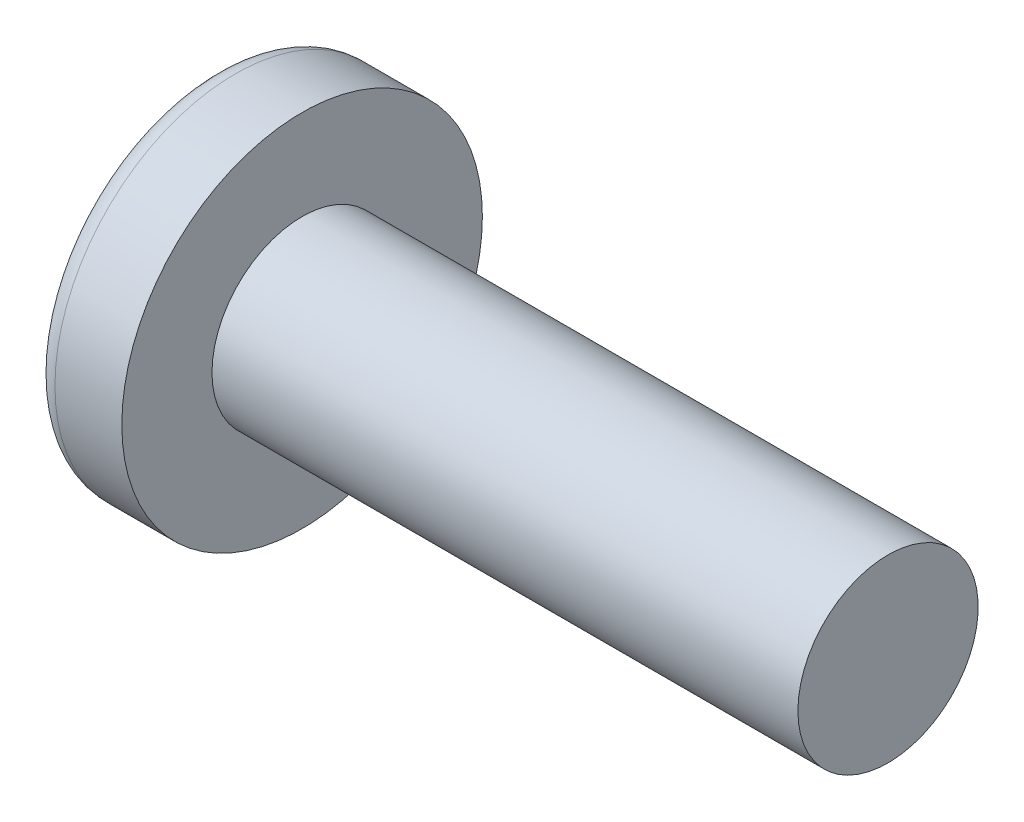
SolidWorks part; units mm, degrees
ref_plane "Plane1" through (0, 0, 0) normal (0, 0, 1) x (1, 0, 0)
ref_plane "Plane2" through (0, 0, 0) normal (0, 1, 0) x (1, 0, 0)
ref_plane "Plane3" through (0, 0, 0) normal (1, 0, 0) x (0, 0, -1)
other "Configuration Table"
sketch "BodySke" plane through (0, 0, 0) normal (0, 0, 1) x (1, 0, 0)
  line L0 (3.1, 2) -> (3.1, 4)
  line L1 (3.8, 6.35) -> (3.8, -3.175) construction
  line L2 (-25.4, 0) -> (127, 0) construction
  line L3 (16.1, 0) -> (0, 0)
  line L4 (3.1, 2) -> (16.1, 2)
  line L5 (16.1, 2) -> (16.1, 0)
  line L6 (1.6164, 4) -> (3.1, 4)
  line L7 (3.1, -2) -> (16.1, -2) construction
  line L8 (3.1, 6.35) -> (3.1, -3.175) construction
  arc A0 (1.227, 3.8007) -> (0, 0) centre (6.5, 0) ccw
  arc A2 (1.227, 3.8007) -> (1.6164, 4) centre (1.6164, 3.52) cw
  dimension "Head_crown_rad" = 6.5
  dimension "Head_fillet_rad" = 0.48
  dimension "Diameter" = 4
  dimension "Length" = 13
  dimension "Head_ht" = 3.1
  dimension "Head_dia" = 8
  dimension "Advance" = 0.7
  dimension "Thread_nom" = 13
revolve "Base-Revolve" add sketch "BodySke" angle 360 about L2
cosmetic thread "ThreadCosmetic" [suppressed] parameters "Thread_length"=12.3, "Thread_minor"=3.22
sketch "Sketch3" plane through (0, 0, 0) normal (1, 0, 0) x (0, 0, -1)
  line L0 (0.465, -2.2) -> (-0.465, -2.2)
  line L1 (0.465, -2.2) -> (0.465, 2.2)
  line L2 (-0.465, 2.2) -> (0.465, 2.2)
  line L3 (-0.465, 2.2) -> (-0.465, -2.2)
  dimension "Cross_dia" = 4.4
  dimension "D1" = 2.2
  dimension "Cross_width" = 0.93
  dimension "D2" = 0.465
ref_plane "Plane4" through (2.45, 0, 0) normal (1, 0, 0) x (0, 0, -1)
sketch "Sketch4" plane through (2.45, 0, 0) normal (1, 0, 0) x (0, 0, -1)
  line L0 (0.2325, -0.2325) -> (-0.2325, -0.2325)
  line L1 (0.2325, -0.2325) -> (0.2325, 0.2325)
  line L2 (-0.2325, 0.2325) -> (0.2325, 0.2325)
  line L3 (-0.2325, 0.2325) -> (-0.2325, -0.2325)
  dimension "D2" = 0.465
  dimension "D1" = 0.465
  dimension "D3" = 0.2325
  dimension "D4" = 0.2325
loft "Cut-Loft1" cut profiles "Sketch3", "Sketch4"
pattern_circular "CirPattern1" count 2 every 90 about axis through (0, 0, 0) along (1, 0, 0) of "Cut-Loft1"
sketch "ThdSchSke" plane through (0, 0, 0) normal (0, 0, 1) x (1, 0, 0)
  line L0 (3.8, -1.61) -> (3.5269, -2)
  line L1 (3.8, -1.61) -> (4.0731, -2)
  line L2 (4.0731, -2) -> (4.0731, -2.5)
  line L3 (-3.175, 0) -> (5.1513, 0) construction
  line L5 (4.0731, -2.5) -> (3.5269, -2.5)
  line L6 (3.5269, -2.5) -> (3.5269, -2)
  dimension "Diameter" = 4
  dimension "SideAngle" = 55
  dimension "VeeAngle" = 70
  dimension "Thread_minor" = 3.22
  dimension "Overcut" = 5
  dimension "Start" = 3.8
revolve "ThreadSchematic" [suppressed] cut sketch "ThdSchSke" angle 360 about L3
pattern_linear "ThdSchPat" [suppressed]
equation "\"D1@Sketch3\" = \"Cross_dia@Sketch3\" / 2"
equation "\"D2@Sketch3\" = \"Cross_width@Sketch3\" / 2"
equation "\"D1@Sketch4\" = \"Cross_width@Sketch3\" *.5"
equation "\"D2@Sketch4\" = \"D1@Sketch4\""
equation "\"D3@Sketch4\" = \"D1@Sketch4\" / 2"
equation "\"D4@Sketch4\" = \"D2@Sketch4\" / 2"
equation "\"Thread_length@ThreadCosmetic\" = ((sgn( (\"Length@BodySke\" - \"Advance@BodySke\" ) - \"Thread_nom@BodySke\" )-1)*( (\"Length@BodySke\" - \"Advance@BodySke\" ) - \"Thread_nom@BodySke\" ))/-2+ \"Thread_nom@BodySke\""
equation "\"Thread_minor@ThdSchSke\" = \"Thread_minor@ThreadCosmetic\""
equation "\"Diameter@ThdSchSke\" = \"Diameter@BodySke\""
equation "\"Overcut@ThdSchSke\" = \"Diameter@BodySke\" * 1.25"
equation "\"Start@ThdSchSke\" = \"Head_ht@BodySke\" + \"Length@BodySke\" - \"Thread_length@ThreadCosmetic\"  '---Non-countersunk---"
equation "\"Num_threads@ThdSchPat\" = int( \"Thread_length@ThreadCosmetic\" / \"Advance@BodySke\" + 0.999 )  + 1"
equation "\"Advance@ThdSchPat\" = \"Thread_length@ThreadCosmetic\" /  (\"Num_threads@ThdSchPat\" - 1) 'relax it"
